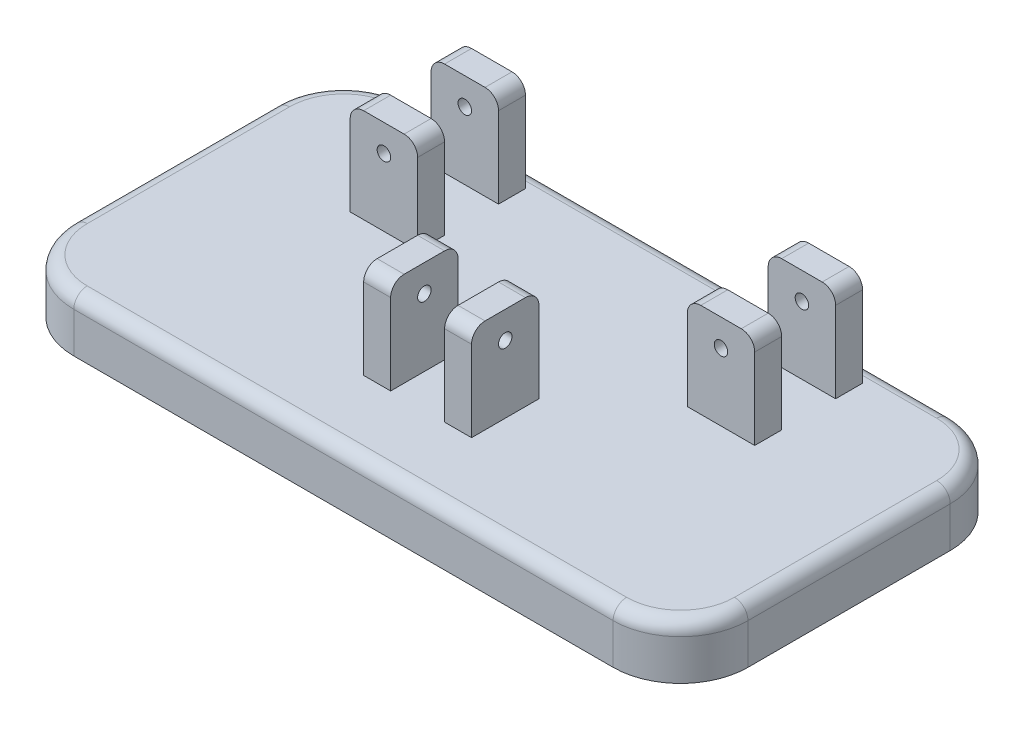
SolidWorks part; units mm, degrees
material "ABS"
ref_plane "Front Plane" through (0, 0, 0) normal (0, 0, 1) x (1, 0, 0)
ref_plane "Top Plane" through (0, 0, 0) normal (0, 1, 0) x (1, 0, 0)
ref_plane "Right Plane" through (0, 0, 0) normal (1, 0, 0) x (0, 0, -1)
sketch "Sketch3" plane through (0, 0, 0) normal (0, 1, 0) x (1, 0, 0)
  line L1 (-40, 25) -> (40, 25)
  line L2 (-50, 15) -> (-50, -15)
  line L3 (-40, -25) -> (40, -25)
  line L4 (50, 15) -> (50, -15)
  line L5 (-50, 25) -> (50, -25) construction
  line L6 (-50, -25) -> (50, 25) construction
  arc A0 (50, -15) -> (40, -25) centre (40, -15) cw
  arc A1 (50, 15) -> (40, 25) centre (40, 15) ccw
  arc A2 (-40, -25) -> (-50, -15) centre (-40, -15) cw
  arc A3 (-50, 15) -> (-40, 25) centre (-40, 15) cw
  point P0 (0, 0)
  dimension "D3" = 10
  dimension "D1" = 100
  dimension "D2" = 50
extrude "Boss-Extrude1" add sketch "Sketch3" along normal blind 8
sketch "Sketch4" plane through (0, 8, 0) normal (0, 1, 0) x (1, 0, 0)
  line L0 (0, -4.4) -> (0, 4.4) construction
  line L1 (-30, 22) -> (-20, 22)
  line L2 (-30, 22) -> (-30, 18)
  line L3 (-30, 18) -> (-20, 18)
  line L4 (-20, 22) -> (-20, 18)
  line L5 (-30, 10) -> (-20, 10)
  line L6 (-30, 10) -> (-30, 6)
  line L7 (-30, 6) -> (-20, 6)
  line L8 (-20, 10) -> (-20, 6)
  line L9 (-8, -4) -> (-4, -4)
  line L10 (-8, -4) -> (-8, -14)
  line L11 (-8, -14) -> (-4, -14)
  line L12 (-4, -4) -> (-4, -14)
  line L13 (8, -14) -> (4, -14)
  line L14 (4, -4) -> (4, -14)
  line L15 (8, -4) -> (4, -4)
  line L16 (8, -4) -> (8, -14)
  line L17 (30, 6) -> (20, 6)
  line L18 (20, 10) -> (20, 6)
  line L19 (30, 10) -> (20, 10)
  line L20 (30, 10) -> (30, 6)
  line L21 (30, 18) -> (20, 18)
  line L22 (20, 22) -> (20, 18)
  line L23 (30, 22) -> (20, 22)
  line L24 (30, 22) -> (30, 18)
  point P8 (-25, 6)
  point P10 (-25, 18)
  dimension "D1" = 10
  dimension "D2" = 4
  dimension "D3" = 4
  dimension "D4" = 10
  dimension "D5" = 8
  dimension "D6" = 6
  dimension "D7" = 25
  dimension "D8" = 25
  dimension "D9" = 10
  dimension "D10" = 4
  dimension "D11" = 4
  dimension "D12" = 4
extrude "Boss-Extrude2" add sketch "Sketch4" along normal blind 14
sketch "Sketch5" plane through (0, 0, -6) normal (0, 0, 1) x (1, 0, 0)
  line L0 (-20, 22) -> (-20, 8) construction
  line L1 (-30, 22) -> (-20, 22) construction
  line L2 (20, 22) -> (30, 22) construction
  line L3 (20, 22) -> (20, 8) construction
  circle A0 centre (-25, 18) radius 1
  circle A1 centre (25, 18) radius 1
  dimension "D1" = 2
  dimension "D2" = 2
  dimension "D3" = 5
  dimension "D4" = 4
  dimension "D5" = 4
  dimension "D6" = 5
extrude "Cut-Extrude1" cut sketch "Sketch5" against normal blind 16
sketch "Sketch6" plane through (-8, 0, 0) normal (-1, 0, 0) x (0, 0, 1)
  line L0 (4, 22) -> (14, 22) construction
  line L1 (14, 22) -> (14, 8) construction
  circle A0 centre (9, 18) radius 1
  dimension "D1" = 2
  dimension "D2" = 4
  dimension "D3" = 5
extrude "Cut-Extrude2" cut sketch "Sketch6" against normal blind 16
fillet "Fillet1" radius 2 20 edges at (-47.0711, 8, -22.0711) (0, 8, -25) (47.0711, 8, -22.0711) (50, 8, 0) (47.0711, 8, 22.0711) (0, 8, 25) (-47.0711, 8, 22.0711) (-50, 8, 0) (6, 22, 14) (6, 22, 4) (-6, 22, 4) (-6, 22, 14) (30, 22, -8) (20, 22, -8) (30, 22, -20) (20, 22, -20) (-20, 22, -8) (-30, 22, -8) (-20, 22, -20) (-30, 22, -20)
